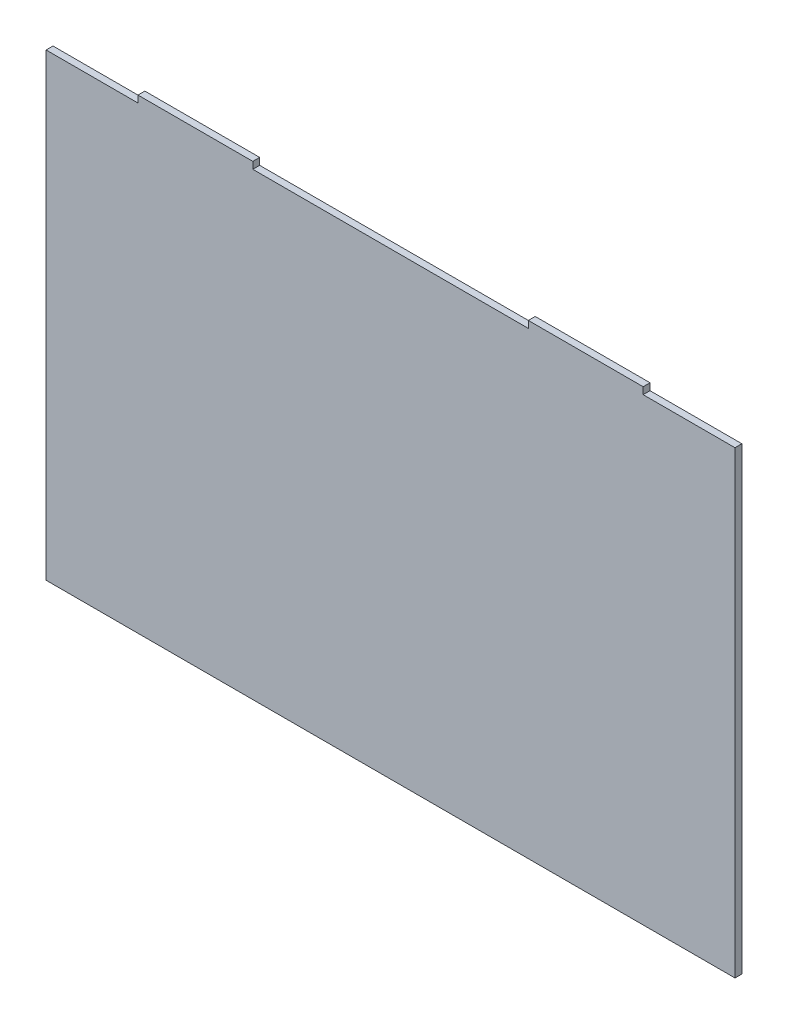
SolidWorks part; units mm, degrees
ref_plane "Plan de face" through (0, 0, 0) normal (0, 0, 1) x (1, 0, 0)
ref_plane "Plan de dessus" through (0, 0, 0) normal (0, 1, 0) x (1, 0, 0)
ref_plane "Plan de droite" through (0, 0, 0) normal (1, 0, 0) x (0, 0, -1)
sketch "Esquisse1" plane through (0, 0, 0) normal (0, 0, 1) x (1, 0, 0)
  line L1 (150, -101.5) -> (-150, -101.5)
  line L2 (150, -101.5) -> (150, 101.5)
  line L3 (150, 101.5) -> (-150, 101.5)
  line L4 (-150, -101.5) -> (-150, 101.5)
  line L5 (150, -101.5) -> (-150, 101.5) construction
  line L6 (150, 101.5) -> (-150, -101.5) construction
  point P0 (0, 0)
  dimension "D1" = 300
  dimension "D2" = 203
extrude "Boss.-Extru.1" add sketch "Esquisse1" along normal blind 3
sketch "Esquisse2" plane through (0, 0, 3) normal (0, 0, 1) x (1, 0, 0)
  line L0 (150, 101.5) -> (-150, 101.5) construction
  line L1 (-150, 101.5) -> (-110, 101.5)
  line L2 (-150, 101.5) -> (-150, 98.5)
  line L3 (-150, 98.5) -> (-110, 98.5)
  line L4 (-110, 101.5) -> (-110, 98.5)
  line L5 (-60, 101.5) -> (60, 101.5)
  line L6 (-60, 101.5) -> (-60, 98.5)
  line L7 (-60, 98.5) -> (60, 98.5)
  line L8 (60, 101.5) -> (60, 98.5)
  line L10 (150, 101.5) -> (110, 101.5)
  line L11 (150, 101.5) -> (150, 98.5)
  line L12 (150, 98.5) -> (110, 98.5)
  line L13 (110, 101.5) -> (110, 98.5)
  dimension "D1" = 40
  dimension "D2" = 3
  dimension "D3" = 3
  dimension "D4" = 3
  dimension "D5" = 40
  dimension "D6" = 50
  dimension "D7" = 50
extrude "Enlèv. mat.-Extru.1" cut sketch "Esquisse2" against normal blind 3
